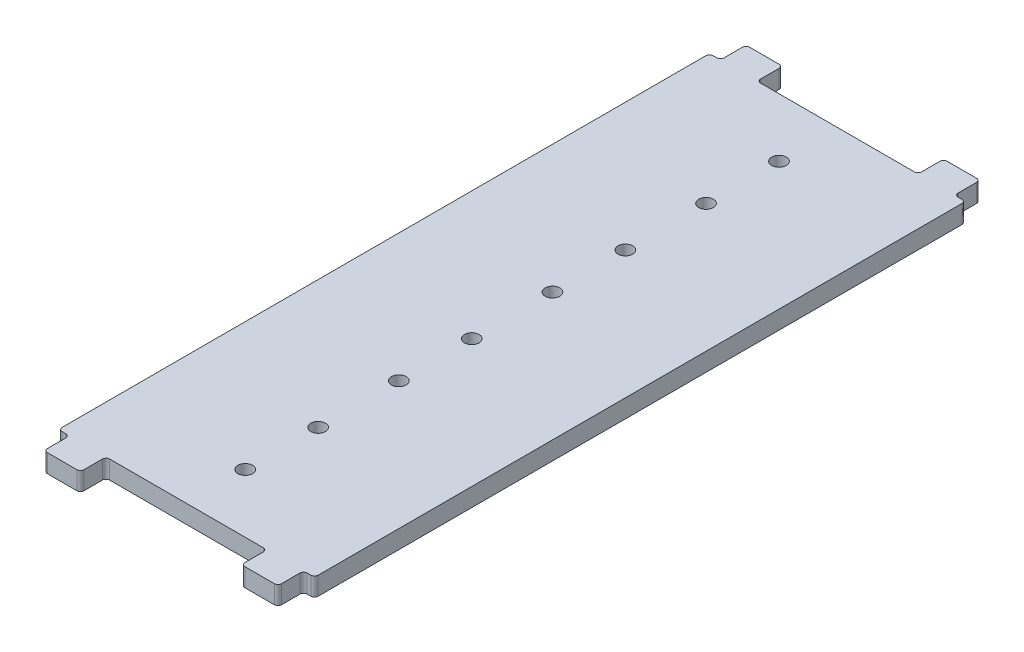
SolidWorks part; units mm, degrees
material "Acrylic (Medium-high impact)"
ref_plane "Front Plane" through (0, 0, 0) normal (0, 0, 1) x (1, 0, 0)
ref_plane "Top Plane" through (0, 0, 0) normal (0, 1, 0) x (1, 0, 0)
ref_plane "Right Plane" through (0, 0, 0) normal (1, 0, 0) x (0, 0, -1)
sketch "Sketch1" plane through (0, 0, 0) normal (0, 1, 0) x (1, 0, 0)
  line L0 (0, 0) -> (0, 34.093) construction
  line L5 (34, -89) -> (33, -89)
  line L6 (35, -88) -> (35, 88)
  line L27 (34, 89) -> (33, 89)
  line L28 (-35, -88) -> (-35, 88)
  line L29 (35, -89) -> (-35, 89) construction
  line L30 (35, 89) -> (-35, -89) construction
  line L32 (-32, 90) -> (-32, 95)
  line L33 (-31, 96) -> (-23, 96)
  line L34 (-22, 90) -> (-22, 95)
  line L35 (0, 0) -> (-23.5471, 0) construction
  line L36 (31, 96) -> (23, 96)
  line L37 (22, 90) -> (22, 95)
  line L38 (32, 90) -> (32, 95)
  line L39 (21, 89) -> (-21, 89)
  line L40 (-33, 89) -> (-34, 89)
  line L41 (32, -90) -> (32, -95)
  line L42 (31, -96) -> (23, -96)
  line L43 (22, -90) -> (22, -95)
  line L44 (-22, -90) -> (-22, -95)
  line L45 (-31, -96) -> (-23, -96)
  line L46 (-32, -90) -> (-32, -95)
  line L47 (-33, -89) -> (-34, -89)
  line L48 (21, -89) -> (-21, -89)
  arc A0 (-34, 89) -> (-35, 88) centre (-34, 88) ccw
  arc A1 (-33, 89) -> (-32, 90) centre (-33, 90) ccw
  arc A2 (-32, 95) -> (-31, 96) centre (-31, 95) cw
  arc A3 (-23, 96) -> (-22, 95) centre (-23, 95) cw
  arc A4 (-21, 89) -> (-22, 90) centre (-21, 90) cw
  arc A5 (22, 90) -> (21, 89) centre (21, 90) cw
  arc A6 (23, 96) -> (22, 95) centre (23, 95) ccw
  arc A7 (31, 96) -> (32, 95) centre (31, 95) cw
  arc A8 (32, 90) -> (33, 89) centre (33, 90) ccw
  arc A9 (35, 88) -> (34, 89) centre (34, 88) ccw
  arc A10 (34, -89) -> (35, -88) centre (34, -88) ccw
  arc A11 (32, -90) -> (33, -89) centre (33, -90) cw
  arc A12 (32, -95) -> (31, -96) centre (31, -95) cw
  arc A13 (23, -96) -> (22, -95) centre (23, -95) cw
  arc A14 (22, -90) -> (21, -89) centre (21, -90) ccw
  arc A15 (-22, -95) -> (-23, -96) centre (-23, -95) cw
  arc A16 (-22, -90) -> (-21, -89) centre (-21, -90) cw
  arc A17 (-34, -89) -> (-35, -88) centre (-34, -88) cw
  arc A18 (-32, -90) -> (-33, -89) centre (-33, -90) ccw
  arc A19 (-31, -96) -> (-32, -95) centre (-31, -95) cw
  point P0 (0, 0)
  point P30 (-32, 89)
  point P33 (-32, 96)
  point P36 (-22, 96)
  point P39 (-22, 89)
  point P42 (22, 89)
  point P45 (22, 96)
  point P48 (32, 96)
  point P51 (32, 89)
  point P60 (32, -89)
  point P63 (32, -96)
  point P66 (22, -96)
  point P69 (22, -89)
  point P72 (-22, -96)
  point P75 (-22, -89)
  point P81 (-32, -89)
  point P84 (-32, -96)
  dimension "D6" = 1
  dimension "D1" = 70
  dimension "D2" = 178
  dimension "D3" = 7
  dimension "D4" = 10
  dimension "D5" = 3
extrude "Boss-Extrude1" add sketch "Sketch1" along normal blind 5
sketch "Sketch2" plane through (0, 5, 0) normal (0, 1, 0) x (1, 0, 0)
  line L0 (21, 89) -> (-21, 89) construction
  circle A0 centre (0, 73) radius 2
  circle A1 centre (0, 53.061) radius 2
  circle A2 centre (0, 11.061) radius 2
  circle A3 centre (0, 31) radius 2
  circle A4 centre (0, -30.939) radius 2
  circle A5 centre (0, -11) radius 2
  circle A8 centre (0, -72.939) radius 2
  circle A9 centre (0, -53) radius 2
  dimension "D1" = 4
  dimension "D2" = 4
  dimension "D3" = 19.939
  dimension "D4" = 16
  dimension "D5" = 4
extrude "Cut-Extrude1" cut sketch "Sketch2" against normal blind 10
